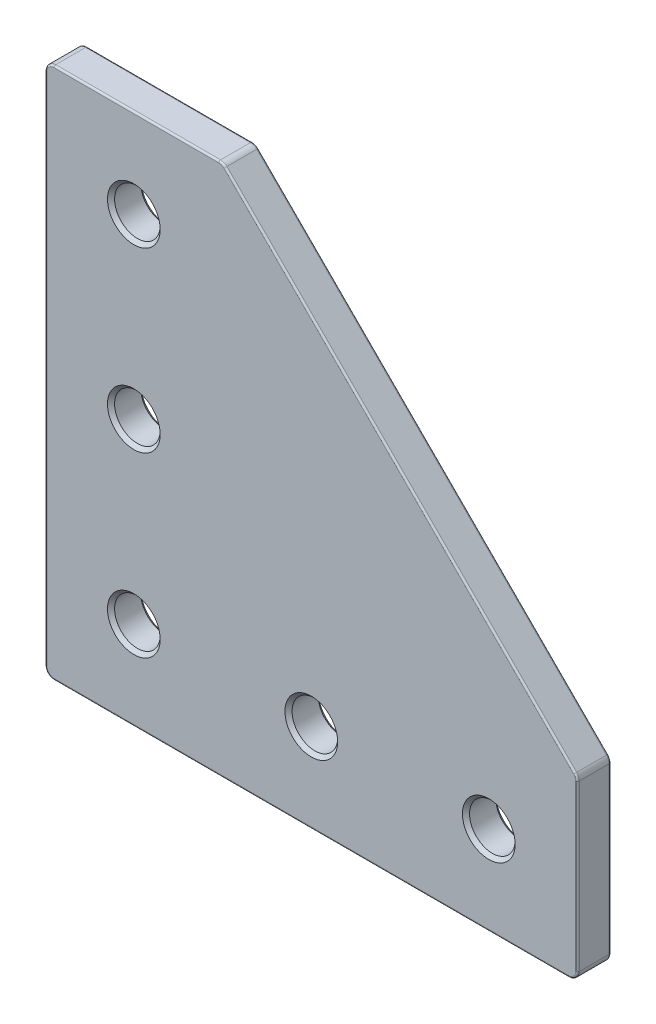
SolidWorks part; units mm, degrees
ref_plane "Front Plane" through (0, 0, 0) normal (0, 0, 1) x (1, 0, 0)
ref_plane "Top Plane" through (0, 0, 0) normal (0, 1, 0) x (1, 0, 0)
ref_plane "Right Plane" through (0, 0, 0) normal (1, 0, 0) x (0, 0, -1)
sketch "Sketch1" plane through (0, 0, 0) normal (0, 0, 1) x (1, 0, 0)
  line L0 (0, -38.1) -> (0, 38.1) construction
  line L1 (-38.1, 38.1) -> (-12.7, 38.1)
  line L2 (-38.1, 38.1) -> (-38.1, -38.1)
  line L3 (38.1, -12.7) -> (38.1, -38.1)
  line L4 (-38.1, -38.1) -> (38.1, -38.1)
  line L5 (-12.7, 38.1) -> (38.1, -12.7)
  line L6 (-25.4, -25.4) -> (-25.4, 0) construction
  line L7 (-25.4, 0) -> (-25.4, 25.4) construction
  line L8 (-25.4, -25.4) -> (0, -25.4) construction
  line L9 (0, -25.4) -> (25.4, -25.4) construction
  line L10 (-28.575, -25.4) -> (-27.305, -25.4) construction
  circle A0 centre (-25.4, -25.4) radius 3.2639
  circle A1 centre (-25.4, -25.4) radius 3.175 construction
  dimension "Mounting Hole Diameter" = 6.5278
  dimension "Mounting Fastener Thread Size" = 6.35
  dimension "Top Flat" = 25.4
  dimension "Side Flat" = 25.4
  dimension "Length" = 76.2
  dimension "Mounting Hole Offset" = 12.7
  dimension "D5" = 12.7
  dimension "Mounting Hole CtoC" = 25.4
  dimension "Mounting Fastener Thread Pitch" = 1.27
sketch "Sketch2" plane through (0, 0, 0) normal (1, 0, 0) x (0, 0, -1)
  line L0 (-2.3876, -25.4) -> (2.3876, -25.4) construction
  line L1 (2.3876, -25.4) -> (10.3124, -25.4) construction
  dimension "Thickness" = 4.7752
  dimension "Mounting Fastener Thread Length" = 12.7
sketch "Sketch3" plane through (0, 0, 0) normal (0, 0, 1) x (1, 0, 0)
  line L0 (-38.1, 38.1) -> (-38.1, -38.1) construction
  line L1 (-38.1, -38.1) -> (38.1, -38.1) construction
  line L2 (38.1, -12.7) -> (38.1, -38.1) construction
  line L3 (-12.7, 38.1) -> (38.1, -12.7) construction
  line L4 (-38.1, 38.1) -> (-12.7, 38.1) construction
  line L5 (-38.1, 38.1) -> (-38.1, -38.1)
  line L6 (-38.1, -38.1) -> (38.1, -38.1)
  line L7 (38.1, -12.7) -> (38.1, -38.1)
  line L8 (-12.7, 38.1) -> (38.1, -12.7)
  line L9 (-38.1, 38.1) -> (-12.7, 38.1)
extrude "Boss-Extrude1" add sketch "Sketch3" along normal up to vertex (2.3876 mm away) from vertex at -2.3876 starting at point (0, -25.4, -2.3876)
sketch "Sketch4" plane through (0, 0, 2.3876) normal (0, 0, 1) x (1, 0, 0)
  circle A0 centre (-25.4, -25.4) radius 3.2639 construction
  circle A1 centre (-25.4, -25.4) radius 3.2639
extrude "Cut-Extrude1" cut sketch "Sketch4" against normal through all both and the other way through all
sketch "Sketch5" plane through (0, 0, 2.3876) normal (0, 0, 1) x (1, 0, 0)
  circle A0 centre (-25.4, -25.4) radius 3.7719
  circle A1 centre (-25.4, -25.4) radius 3.2639 construction
  dimension "D1" = 0.508
extrude "Cut-Extrude2" cut sketch "Sketch5" against normal through all draft 45
sketch "Sketch6" plane through (0, 0, -2.3876) normal (0, 0, -1) x (-1, 0, 0)
  circle A1 centre (25.4, -25.4) radius 3.7719
  circle A2 centre (25.4, -25.4) radius 3.7719
  dimension "D1" = 0
extrude "Cut-Extrude3" cut sketch "Sketch6" against normal through all draft 45
pattern_linear "LPattern1" count 3 spacing 25.4 along (0, 1, 0) of "Cut-Extrude1", "Cut-Extrude2", "Cut-Extrude3"
pattern_circular "CirPattern1" count 2 every 90 about axis through (-25.4, -25.4, 0) along (0, 0, 1) of "LPattern1"
fillet "Fillet1" radius 1.27 5 edges at (38.1, -12.7, 0) (38.1, -38.1, 0) (-38.1, -38.1, 0) (-38.1, 38.1, 0) (-12.7, 38.1, 0)
fillet "Fillet2" radius 0.254 20 edges at (-12.74, 38.0033, -2.3876) (12.7, 12.7, -2.3876) (38.0033, -12.74, -2.3876) (38.1, -25.028, -2.3876) (37.728, -37.728, -2.3876) (0, -38.1, -2.3876) (-37.728, -37.728, -2.3876) (-38.1, 0, -2.3876) (-37.728, 37.728, -2.3876) (-12.74, 38.0033, 2.3876) (12.7, 12.7, 2.3876) (38.0033, -12.74, 2.3876) (38.1, -25.028, 2.3876) (37.728, -37.728, 2.3876) (0, -38.1, 2.3876) (-37.728, -37.728, 2.3876) (-38.1, 0, 2.3876) (-37.728, 37.728, 2.3876) (-25.028, 38.1, -2.3876) (-25.028, 38.1, 2.3876)
equation "\"D5@Sketch1\" = \"Mounting Hole Offset@Sketch1\""
equation "\"D3@LPattern1\"=\"Mounting Hole CtoC@Sketch1\""
